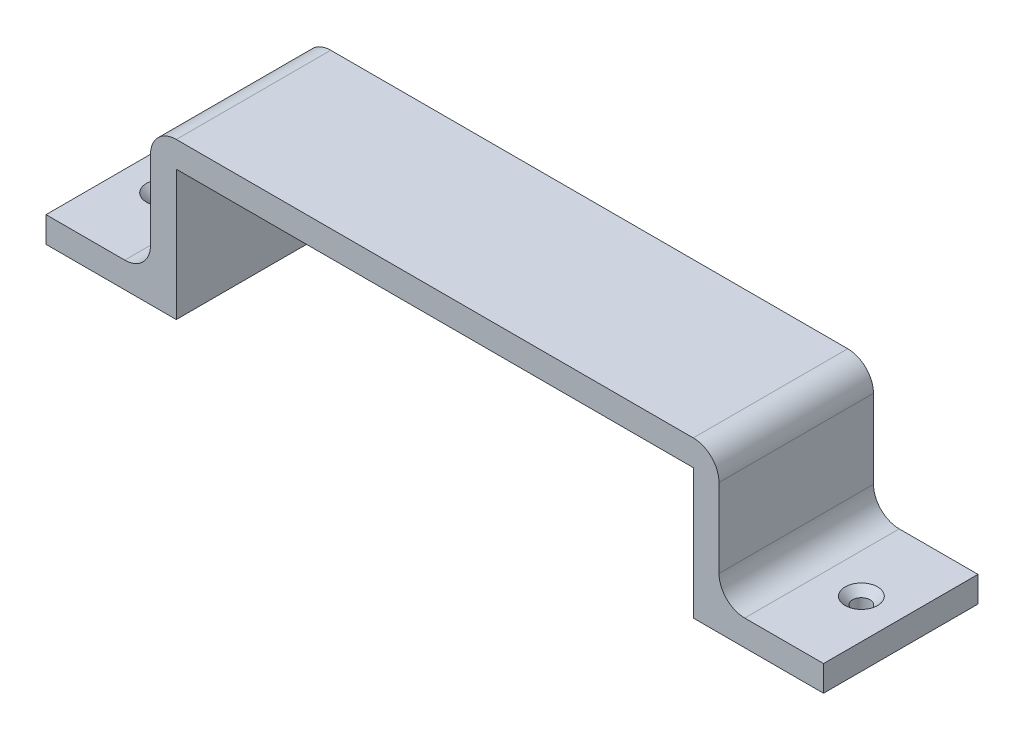
SolidWorks part; units mm, degrees
ref_plane "Plan de face" through (0, 0, 0) normal (0, 0, 1) x (1, 0, 0)
ref_plane "Plan de dessus" through (0, 0, 0) normal (0, 1, 0) x (1, 0, 0)
ref_plane "Plan de droite" through (0, 0, 0) normal (1, 0, 0) x (0, 0, -1)
sketch "Esquisse1" plane through (0, 0, 0) normal (0, 0, 1) x (1, 0, 0)
  line L0 (-50.2, 0) -> (50.2, 0)
  line L1 (-50.2, 0) -> (-50.2, -25.3)
  line L2 (-50.2, -25.3) -> (-75.5, -25.3)
  line L3 (0, -55) -> (0, 55) construction
  line L4 (50.2, 0) -> (50.2, -25.3)
  line L5 (50.2, -25.3) -> (75.5, -25.3)
  line L6 (-55.2, -20.3) -> (-75.5, -20.3)
  line L7 (-55.2, 5) -> (-55.2, -20.3)
  line L8 (-55.2, 5) -> (55.2, 5)
  line L9 (55.2, 5) -> (55.2, -20.3)
  line L10 (55.2, -20.3) -> (75.5, -20.3)
  line L11 (-75.5, -25.3) -> (-75.5, -20.3)
  line L12 (75.5, -25.3) -> (75.5, -20.3)
  point P4 (0, 0)
  dimension "D1" = 100.4
  dimension "D2" = 25.3
  dimension "D3" = 5
extrude "Boss.-Extru.1" add sketch "Esquisse1" along normal blind 30
fillet "Congé1" radius 5 4 edges at (55.2, -20.3, 15) (55.2, 5, 15) (-55.2, 5, 15) (-55.2, -20.3, 15)
hole_wizard "Fraisage pour vis à tête fraisée M31" positions "Esquisse2" profile "Esquisse3" countersink size "M3" standard "Ansi Metric" end condition through all
sketch "Esquisse2" plane through (0, -20.3, 0) normal (0, 1, 0) x (1, 0, 0)
  point P0 (-67.85, -15)
  point P2 (67.85, -15)
sketch "Esquisse3" plane through (-67.85, -20.3, 15) normal (1, 0, 0) x (0, 0, 1)
  line L0 (0, 0) -> (0, 5)
  line L1 (0, 5) -> (1.7, 5)
  line L2 (1.7, 5) -> (1.7, 1.45)
  line L3 (1.7, 1.45) -> (3.15, 0)
  line L5 (3.15, 0) -> (0, 0)
  line L6 (-1.7, 1.45) -> (-3.15, 0) construction
  line L11 (0, -6.35) -> (0, 107.95) construction
  dimension "Diamètre du perçage jusqu'au prochain" = 3.4
  dimension "Profondeur du perçage jusqu'au prochain" = 5
  dimension "Diamètre du fraisage entrant" = 6.3
  dimension "Angle du fraisage entrant" = 90
